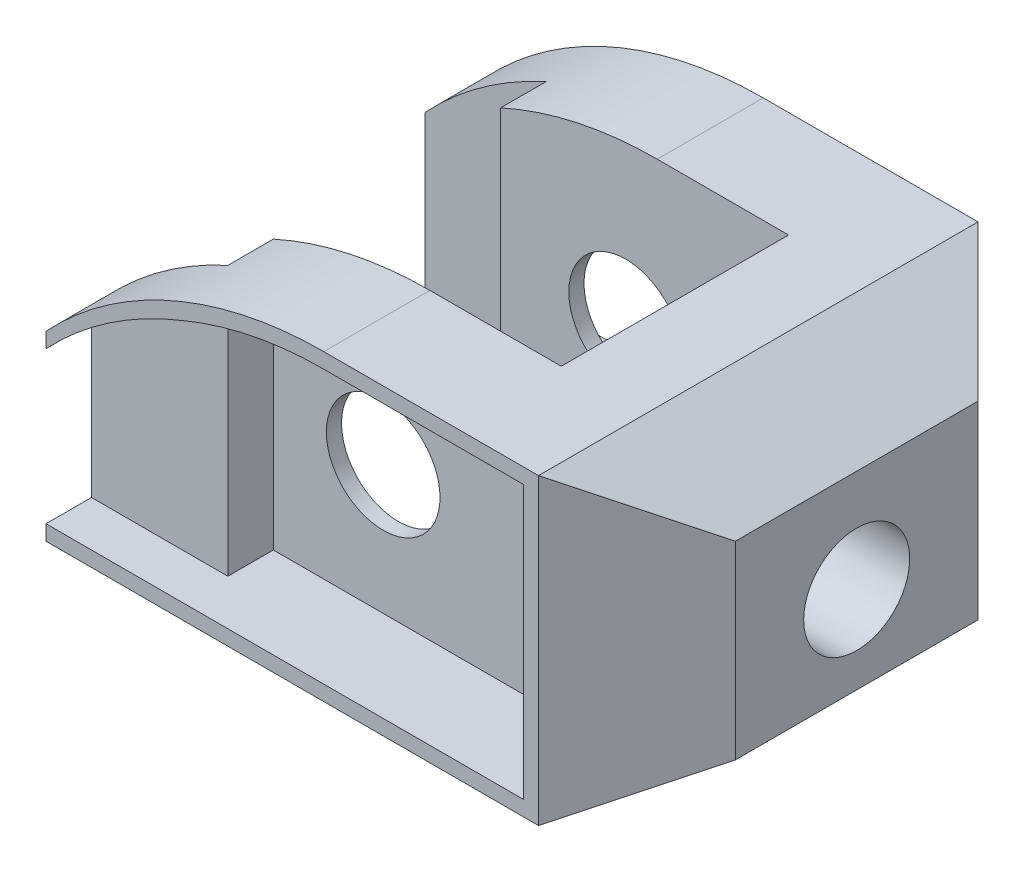
SolidWorks part; units mm, degrees
material "1060 Alloy"
ref_plane "Front Plane" through (0, 0, 0) normal (0, 0, 1) x (1, 0, 0)
ref_plane "Top Plane" through (0, 0, 0) normal (0, 1, 0) x (1, 0, 0)
ref_plane "Right Plane" through (0, 0, 0) normal (1, 0, 0) x (0, 0, -1)
sketch "Sketch1" plane through (0, 0, 0) normal (0, 0, 1) x (1, 0, 0)
  line L0 (0, 13.8138) -> (0, -28.7241) construction
  line L1 (32.5, -19) -> (-32.5, -19)
  line L2 (-32.5, -19) -> (-32.5, 5)
  line L3 (32.5, -19) -> (45.4904, -11.5)
  line L4 (45.4904, -11.5) -> (45.4904, 13.5)
  line L5 (45.4904, 13.5) -> (32.5, 21)
  line L6 (32.5, 21) -> (4.1606, 21)
  circle A0 centre (0, 0) radius 7.5
  arc A1 (-32.5, 5) -> (4.1606, 21) centre (4.1606, -29) cw
  point P8 (0, -19)
  dimension "D1" = 15
  dimension "D9" = 50
  dimension "D2" = 65
  dimension "D3" = 19
  dimension "D4" = 24
  dimension "D5" = 15
  dimension "D6" = 30
  dimension "D7" = 30
  dimension "D8" = 40
extrude "Boss-Extrude1" add sketch "Sketch1" along normal blind 58
sketch "Sketch2" plane through (0, 21, 0) normal (0, 1, 0) x (1, 0, 0)
  line L0 (45.4904, -29) -> (21.5, -29) construction
  line L1 (45.4904, -58) -> (45.4904, 0) construction
  line L2 (-32.5, -58) -> (-32.5, 0) construction
  line L3 (4.1606, -58) -> (4.1606, 0) construction
  line L4 (21.5, -44) -> (-16.5, -44)
  line L5 (21.5, -44) -> (21.5, -14)
  line L6 (21.5, -14) -> (-16.5, -14)
  line L7 (-16.5, -44) -> (-16.5, -14)
  line L8 (-16.5, -29) -> (-32.5, -29) construction
  line L9 (32.5, 0) -> (4.1606, 0) construction
  line L10 (32.5, -58) -> (32.5, 0) construction
  line L11 (32.5, -58) -> (4.1606, -58) construction
  point P6 (4.1606, -29)
  dimension "D1" = 11
  dimension "D2" = 16
  dimension "D3" = 14
  dimension "D4" = 14
extrude "Cut-Extrude1" cut sketch "Sketch2" against normal through all both and the other way through all
sketch "Sketch3" plane through (0, 21, 0) normal (0, 1, 0) x (1, 0, 0)
  line L0 (-32.5, -29) -> (45.4904, -29) construction
  line L1 (-32.5, -58) -> (-32.5, 0) construction
  line L2 (45.4904, -58) -> (45.4904, 0) construction
  line L3 (-16.5, -50) -> (-32.5, -50)
  line L4 (-16.5, -14) -> (-32.5, -14)
  line L5 (-16.5, -14) -> (-16.5, -8)
  line L6 (-16.5, -8) -> (-32.5, -8)
  line L7 (-32.5, -14) -> (-32.5, -8)
  line L8 (-32.5, -44) -> (-32.5, -50)
  line L9 (-16.5, -44) -> (-32.5, -44)
  line L10 (-16.5, -44) -> (-16.5, -50)
  dimension "D1" = 6
extrude "Cut-Extrude4" cut sketch "Sketch3" against normal through all both and the other way through all
sketch "Sketch4" plane through (45.4904, 0, 0) normal (1, 0, 0) x (0, 0, -1)
  line L0 (-58, -19) -> (0, -19) construction
  line L1 (-58, -11.5) -> (-58, 13.5) construction
  circle A0 centre (-29, 0) radius 7
  dimension "D1" = 14
  dimension "D2" = 19
  dimension "D3" = 29
extrude "Cut-Extrude5" cut sketch "Sketch4" against normal through all both and the other way through all
sketch "Sketch6" plane through (0, 21, 0) normal (0, 1, 0) x (1, 0, 0)
  line L0 (32.5, 0) -> (45.4904, -12.9904)
  line L1 (45.4904, -58) -> (45.4904, 0) construction
  line L2 (45.4904, -12.9904) -> (45.4904, 0)
  line L3 (45.4904, 0) -> (32.5, 0)
  line L4 (45.4904, -29) -> (32.5, -29) construction
  line L5 (32.5, -58) -> (32.5, 0) construction
  line L6 (45.4904, -45.0096) -> (45.4904, -58)
  line L7 (32.5, -58) -> (45.4904, -45.0096)
  line L8 (45.4904, -58) -> (32.5, -58)
  dimension "D1" = 45
extrude "Cut-Extrude6" cut sketch "Sketch6" against normal through all both and the other way through all
sketch "Sketch9" plane through (0, 0, 58) normal (0, 0, 1) x (1, 0, 0)
  line L6 (-32.5, -19) -> (32.5, -19)
  line L7 (32.5, -19) -> (32.5, 21)
  line L8 (32.5, 21) -> (4.1606, 21)
  line L9 (-32.5, 5) -> (-32.5, -19)
  line L10 (-32.5, -19) -> (32.5, -19)
  line L11 (32.5, -19) -> (32.5, 21)
  line L12 (-14.5, 15.2242) -> (-14.5, -17)
  line L13 (32.5, 21) -> (4.1606, 21)
  line L14 (-32.5, 5) -> (-32.5, -19)
  line L16 (30.5, -17) -> (30.5, 19)
  line L17 (-30.5, -17) -> (30.5, -17)
  line L18 (-30.5, 4.2061) -> (-30.5, -17)
  line L19 (30.5, 19) -> (4.1606, 19)
  line L20 (30.5, -17) -> (30.5, 19)
  line L21 (-14.5, -17) -> (30.5, -17)
  line L23 (30.5, 19) -> (4.1606, 19)
  arc A1 (4.1606, 21) -> (-32.5, 5) centre (4.1606, -29) ccw
  arc A2 (4.1606, 21) -> (-32.5, 5) centre (4.1606, -29) ccw
  arc A5 (4.1606, 19) -> (-30.5, 4.2061) centre (4.1606, -29) ccw
  arc A6 (4.1606, 19) -> (-14.5, 15.2242) centre (4.1606, -29) ccw
  circle M13 centre (0, 0) radius 7.5
  dimension "D2" = 18
  dimension "D3" = 0
  dimension "D1" = 2
extrude "Cut-Extrude10" cut sketch "Sketch9" against normal blind 12 contours L23 A6 L12 L21 L20 M13
sketch "Sketch10" plane through (0, 0, 58) normal (0, 0, 1) x (1, 0, 0)
  line L0 (-14.5, 15.2242) -> (-14.5, -17)
  line L1 (-14.5, -17) -> (-32.5, -17)
  line L2 (-32.5, 5) -> (-32.5, -19) construction
  line L3 (-32.5, -17) -> (-32.5, 3)
  arc A0 (-32.5, 3) -> (-14.5, 15.2242) centre (3.7054, -30.9475) cw
  arc A1 (4.1606, 21) -> (-32.5, 5) centre (4.1606, -29) ccw construction
  dimension "D2" = 2
  dimension "D1" = 2
extrude "Cut-Extrude12" cut sketch "Sketch10" against normal blind 6
sketch "Sketch14" plane through (0, 0, 0) normal (0, 0, -1) x (-1, 0, 0)
  line L0 (32.5, 5) -> (32.5, -19) construction
  line L11 (14.5, -17) -> (14.5, 15.2242)
  line L15 (30.5, -17) -> (30.5, 4.2061)
  line L16 (-30.5, -17) -> (30.5, -17)
  line L17 (-30.5, 19) -> (-30.5, -17)
  line L18 (-4.1606, 19) -> (-30.5, 19)
  line L20 (-30.5, -17) -> (14.5, -17)
  line L21 (-30.5, 19) -> (-30.5, -17)
  line L22 (-4.1606, 19) -> (-30.5, 19)
  arc A5 (30.5, 4.2061) -> (-4.1606, 19) centre (-4.1606, -29) ccw
  arc A6 (14.5, 15.2242) -> (-4.1606, 19) centre (-4.1606, -29) ccw
  dimension "D2" = 18
  dimension "D1" = 2
extrude "Cut-Extrude13" cut sketch "Sketch14" against normal blind 12
sketch "Sketch15" plane through (0, 0, 0) normal (0, 0, -1) x (-1, 0, 0)
  line L0 (14.5, 15.2242) -> (14.5, -17)
  line L1 (14.5, -17) -> (32.5, -17)
  line L2 (32.5, -17) -> (32.5, 1.9729)
  line L3 (32.5, 5) -> (32.5, -19) construction
  arc A0 (32.5, 1.9729) -> (14.5, 15.2242) centre (-5.3585, -30.6015) ccw
  arc A1 (32.5, 5) -> (-4.1606, 21) centre (-4.1606, -29) ccw construction
  dimension "D1" = 2
extrude "Cut-Extrude14" cut sketch "Sketch15" against normal blind 6
equation "\"A\"= 58mm"
equation "\"B\"= 40mm"
equation "\"C\"= 65mm"
equation "\"D2@Sketch1\"=\"C\""
equation "\"D8@Sketch1\"=\"B\""
equation "\"D3@Sketch4\"=\"A\"/2"
